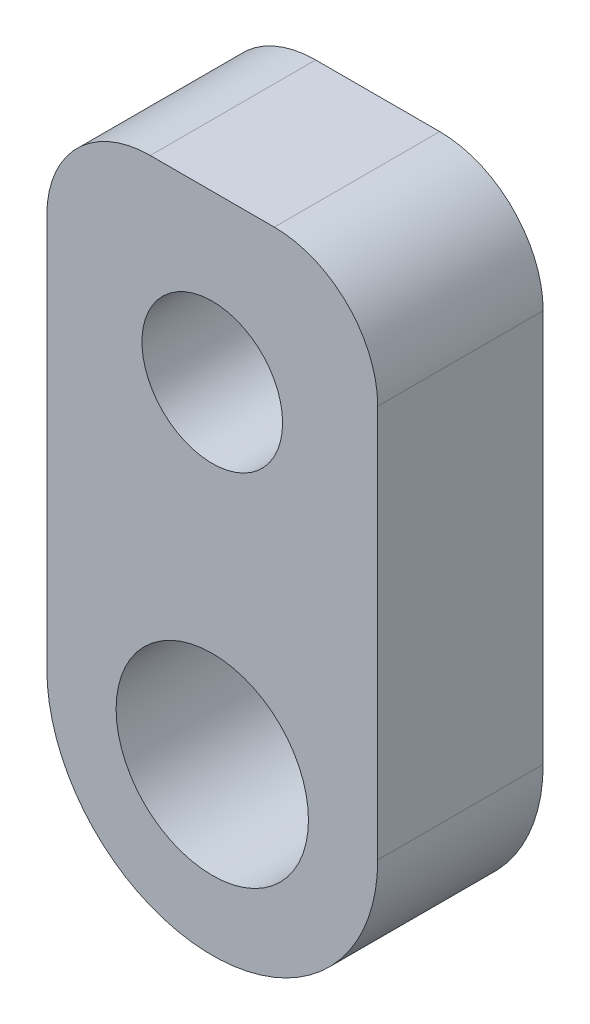
SolidWorks part; units mm, degrees
material "ABS"
ref_plane "Front Plane" through (0, 0, 0) normal (0, 0, 1) x (1, 0, 0)
ref_plane "Top Plane" through (0, 0, 0) normal (0, 1, 0) x (1, 0, 0)
ref_plane "Right Plane" through (0, 0, 0) normal (1, 0, 0) x (0, 0, -1)
sketch "Sketch1" plane through (0, 0, 0) normal (0, 0, 1) x (1, 0, 0)
  circle A0 centre (0, 0) radius 4
  dimension "D1" = 8
sketch "Sketch3" plane through (0, 0, 0) normal (0, 0, 1) x (1, 0, 0)
  line L1 (-4, 12) -> (4, 12)
  line L2 (-4, 12) -> (-4, 0)
  line L3 (-4, 0) -> (4, 0)
  line L4 (4, 12) -> (4, 0)
  circle A0 centre (0, 0) radius 4 construction
  point P4 (0, 0)
  point P6 (0, 4)
  dimension "D1" = 8
  dimension "D2" = 8
sketch "Sketch4" plane through (0, 0, 0) normal (0, 0, 1) x (1, 0, 0)
  line L0 (0, 4) -> (0, 12) construction
  line L1 (-4, 12) -> (4, 12) construction
  circle A0 centre (0, 8) radius 1.7
  point P7 (0, 8)
  dimension "D1" = 3.4
extrude "Boss-Extrude1" add sketch "Sketch1" along normal blind 4
extrude "Boss-Extrude2" add sketch "Sketch3" along normal blind 4
sketch "Sketch2" plane through (0, 0, 0) normal (0, 0, 1) x (1, 0, 0)
  circle A0 centre (0, 0) radius 2.325
  dimension "D1" = 4.65
extrude "Cut-Extrude2" cut sketch "Sketch2" along normal through all
extrude "Cut-Extrude3" cut sketch "Sketch4" along normal blind 4
fillet "Fillet1" radius 2.5 2 edges at (4, 12, 2) (-4, 12, 2)
